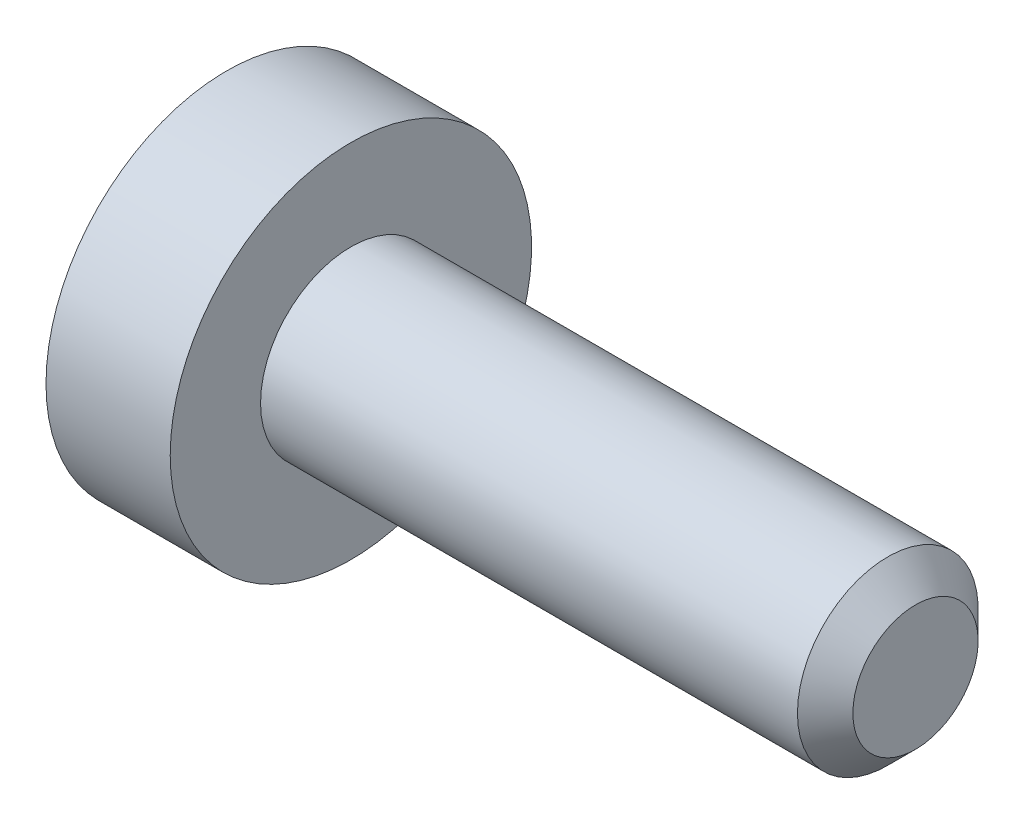
SolidWorks part; units mm, degrees
material "AISI 304"
ref_plane "正面" through (0, 0, 0) normal (0, 0, 1) x (1, 0, 0)
ref_plane "平面" through (0, 0, 0) normal (0, 1, 0) x (1, 0, 0)
ref_plane "右側面" through (0, 0, 0) normal (1, 0, 0) x (0, 0, -1)
ref_plane "Plane1" through (0, 0, 0) normal (0, 0, 1) x (1, 0, 0)
sketch "Sketch1" plane through (0, 0, 0) normal (0, 0, 1) x (1, 0, 0)
  line L0 (0, 0) -> (0, 0.8)
  line L1 (0, 0.8) -> (4.7545, 0.8)
  line L2 (4.7545, 0.8) -> (5, 0.5545)
  line L3 (5, 0.5545) -> (5, 0)
  line L4 (5, 0) -> (0, 0)
  line L5 (5, 0) -> (0, 0) construction
  dimension "D1" = 0.8
revolve "Revolve1" add sketch "Sketch1" angle 360 about L5
cosmetic thread "Cosmetic Thread1" parameters "D1"=3.8, "D2"=1.509
ref_plane "Plane2" through (0, 0, 0) normal (0, 0, 1) x (1, 0, 0)
sketch "Sketch2" plane through (0, 0, 0) normal (0, 0, 1) x (1, 0, 0)
  line L0 (-1.1, 0) -> (-1.1, 1.6)
  line L1 (-1.1, 1.6) -> (0, 1.6)
  line L2 (0, 1.6) -> (0, 0)
  line L3 (0, 0) -> (-1.1, 0)
  line L4 (0, 0) -> (-1.1, 0) construction
revolve "Revolve2" add sketch "Sketch2" angle 360 about L4
ref_plane "Plane3" through (0, 0, 0) normal (0, 0, 1) x (1, 0, 0)
sketch "Sketch3" plane through (0, 0, 0) normal (0, 0, 1) x (1, 0, 0)
  line L0 (-1.1, 0) -> (-1.1, 0.78)
  line L1 (-1.1, 0.78) -> (-0.97, 0.65)
  line L2 (-0.97, 0.65) -> (0.1, 0.65)
  line L3 (0.1, 0.65) -> (0.4753, 0)
  line L4 (0.4753, 0) -> (-1.1, 0)
  line L5 (0.4753, 0) -> (-1.1, 0) construction
revolve "Cut-Revolve1" cut sketch "Sketch3" angle 360 about L5
ref_plane "Plane4" through (-1.1, 0, 0) normal (1, 0, 0) x (0, 0, -1)
sketch "Sketch4" plane through (-1.1, 0, 0) normal (1, 0, 0) x (0, 0, -1)
  line L0 (-0.65, -0.3753) -> (0, -0.7506)
  line L1 (0, -0.7506) -> (0.65, -0.3753)
  line L2 (0.65, -0.3753) -> (0.65, 0.3753)
  line L3 (0.65, 0.3753) -> (0, 0.7506)
  line L4 (0, 0.7506) -> (-0.65, 0.3753)
  line L5 (-0.65, 0.3753) -> (-0.65, -0.3753)
extrude "Cut-Extrude1" cut sketch "Sketch4" along normal blind 1.2
